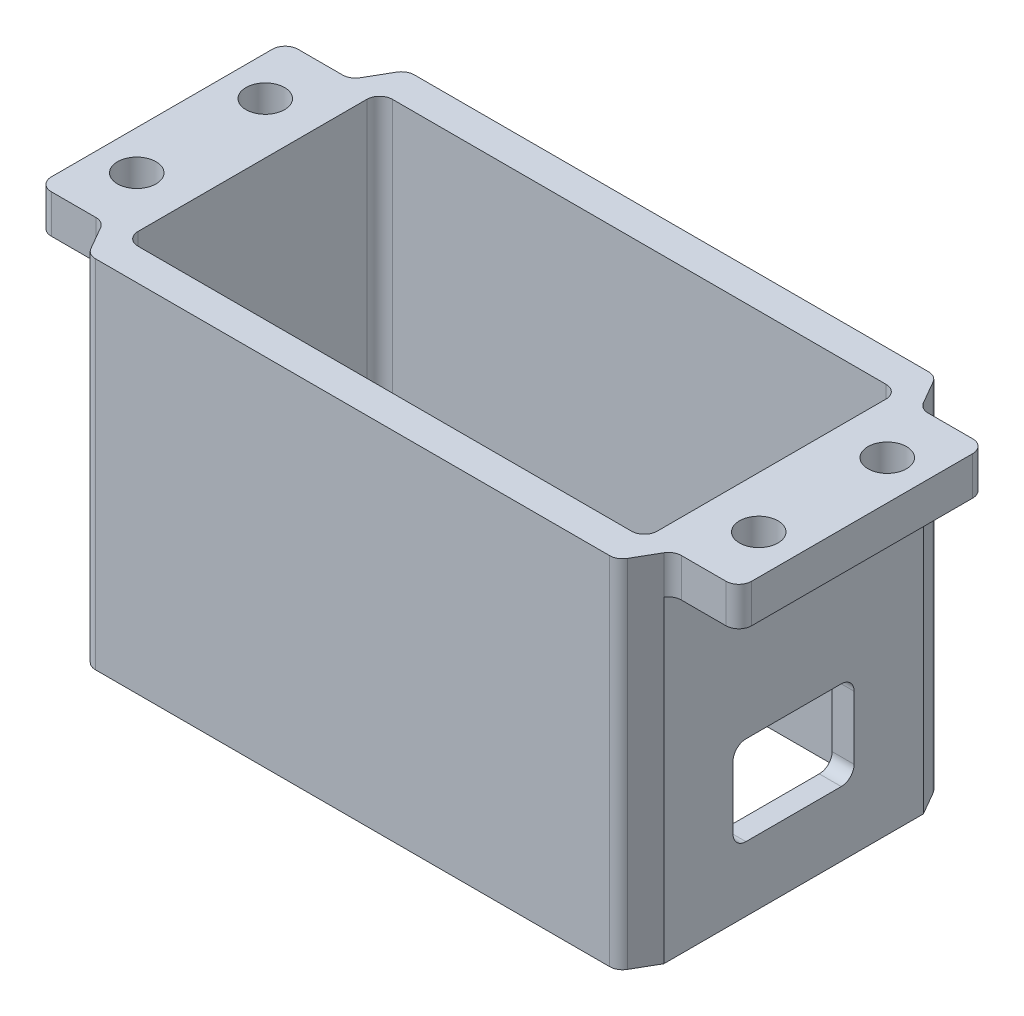
SolidWorks part; units mm, degrees
ref_plane "Piano frontale" through (0, 0, 0) normal (0, 0, 1) x (1, 0, 0)
ref_plane "Piano superiore" through (0, 0, 0) normal (0, 1, 0) x (1, 0, 0)
ref_plane "Piano destro" through (0, 0, 0) normal (1, 0, 0) x (0, 0, -1)
sketch "Schizzo3" plane through (0, -1.8, 0) normal (0, 1, 0) x (1, 0, 0)
  line L20 (27.25, -1.6) -> (27.25, -8.6)
  line L21 (27.25, -1.6) -> (27.25, 1.6)
  line L22 (27.25, 8.6) -> (27.25, 1.6)
  line L23 (22.7774, 9.6) -> (26.25, 9.6)
  line L24 (21.9113, 10.1) -> (20.8721, 11.9)
  line L25 (-20.0061, 12.4) -> (20.0061, 12.4)
  line L26 (-21.9113, 10.1) -> (-20.8721, 11.9)
  line L27 (-26.25, 9.6) -> (-22.7774, 9.6)
  line L28 (-27.25, 1.6) -> (-27.25, 8.6)
  line L29 (-27.25, 1.6) -> (-27.25, -1.6)
  line L30 (-27.25, -8.6) -> (-27.25, -1.6)
  line L31 (-22.7774, -9.6) -> (-26.25, -9.6)
  line L32 (26.25, -9.6) -> (22.7774, -9.6)
  line L34 (-21.9113, -10.1) -> (-20.8721, -11.9)
  line L35 (-20.0061, -12.4) -> (20.0061, -12.4)
  line L36 (21.9113, -10.1) -> (20.8721, -11.9)
  line L38 (-19.2, -9.9) -> (19.2, -9.9)
  line L39 (20.2, -8.9) -> (20.2, 8.9)
  line L40 (-19.2, 9.9) -> (19.2, 9.9)
  line L41 (-20.2, 8.9) -> (-20.2, -8.9)
  arc A14 (27.25, 8.6) -> (26.25, 9.6) centre (26.25, 8.6) ccw
  arc A15 (21.9113, 10.1) -> (22.7774, 9.6) centre (22.7774, 10.6) ccw
  arc A16 (20.8721, 11.9) -> (20.0061, 12.4) centre (20.0061, 11.4) ccw
  arc A17 (-20.0061, 12.4) -> (-20.8721, 11.9) centre (-20.0061, 11.4) ccw
  arc A18 (-22.7774, 9.6) -> (-21.9113, 10.1) centre (-22.7774, 10.6) ccw
  arc A19 (-26.25, 9.6) -> (-27.25, 8.6) centre (-26.25, 8.6) ccw
  arc A20 (-27.25, -8.6) -> (-26.25, -9.6) centre (-26.25, -8.6) ccw
  arc A22 (26.25, -9.6) -> (27.25, -8.6) centre (26.25, -8.6) ccw
  arc A23 (19.2, -9.9) -> (20.2, -8.9) centre (19.2, -8.9) ccw
  arc A24 (-21.9113, -10.1) -> (-22.7774, -9.6) centre (-22.7774, -10.6) ccw
  arc A25 (-20.8721, -11.9) -> (-20.0061, -12.4) centre (-20.0061, -11.4) ccw
  arc A26 (20.0061, -12.4) -> (20.8721, -11.9) centre (20.0061, -11.4) ccw
  arc A27 (22.7774, -9.6) -> (21.9113, -10.1) centre (22.7774, -10.6) ccw
  arc A28 (20.2, 8.9) -> (19.2, 9.9) centre (19.2, 8.9) ccw
  arc A29 (-19.2, 9.9) -> (-20.2, 8.9) centre (-19.2, 8.9) ccw
  arc A30 (-20.2, -8.9) -> (-19.2, -9.9) centre (-19.2, -8.9) ccw
  circle A34 centre (24.2, -5) radius 1.5
  circle A35 centre (24.2, 5) radius 1.5
  circle A36 centre (-24.2, 5) radius 1.5
  circle A37 centre (-24.2, -5) radius 1.5
extrude "Estrusione-Estrusione2" add sketch "Schizzo3" against normal offset from surface (27.7 mm away) 3
sketch "Schizzo4" plane through (27.25, 0, 0) normal (1, 0, 0) x (0, 0, -1)
  line L1 (-3.7102, -17.5388) -> (3.7102, -17.5388)
  line L2 (-4.7102, -18.5388) -> (-4.7102, -23.4612)
  line L3 (-3.7102, -24.4612) -> (3.7102, -24.4612)
  line L4 (4.7102, -18.5388) -> (4.7102, -23.4612)
  line L5 (-4.7102, -17.5388) -> (4.7102, -24.4612) construction
  line L6 (-4.7102, -24.4612) -> (4.7102, -17.5388) construction
  arc A0 (-3.7102, -17.5388) -> (-4.7102, -18.5388) centre (-3.7102, -18.5388) ccw
  arc A1 (-4.7102, -23.4612) -> (-3.7102, -24.4612) centre (-3.7102, -23.4612) ccw
  arc A2 (3.7102, -24.4612) -> (4.7102, -23.4612) centre (3.7102, -23.4612) ccw
  arc A3 (3.7102, -17.5388) -> (4.7102, -18.5388) centre (3.7102, -18.5388) cw
  point P0 (0, -21)
  dimension "D1" = 1
extrude "Taglio-Estrusione1" cut sketch "Schizzo4" against normal up to next
sketch "Schizzo5" plane through (0, -1.8, 0) normal (0, 1, 0) x (1, 0, 0)
  line L0 (27.25, 8.6) -> (27.25, -8.6)
  line L1 (0, 12.4) -> (0, -12.4) construction
  line L7 (20.0061, 12.4) -> (-20.0061, 12.4) construction
  line L8 (-20.0061, -12.4) -> (20.0061, -12.4) construction
  line L17 (21.9113, -9.6) -> (21.9113, 9.6)
  line L19 (22.605, 8.8985) -> (22.605, -8.8985) construction
  line L20 (21.9113, 10.1) -> (20.8721, 11.9) construction
  line L21 (20.8721, -11.9) -> (21.9113, -10.1) construction
  line L22 (21.9113, 10.1) -> (21.9113, -10.1) construction
  line L23 (-21.9113, 10.1) -> (-21.9113, -10.1) construction
  line L25 (21.9113, -9.6) -> (21.9113, -11.3707)
  line L26 (21.9113, -11.3707) -> (27.5074, -11.3707)
  line L27 (27.5074, -11.3707) -> (27.25, -8.6)
  line L28 (21.9113, 9.6) -> (21.9113, 11.6657)
  line L29 (21.9113, 11.6657) -> (27.25, 11.5037)
  line L30 (27.25, 11.5037) -> (27.25, 8.6)
extrude "Taglio-Estrusione2" cut sketch "Schizzo5" against normal up to surface (24.7 mm away) from offset 3 up to face at (0, -29.5, 0) offset against normal yes
mirror "Specchia1" about plane through (0, 0, 0) normal (1, 0, 0) of "Taglio-Estrusione2"
